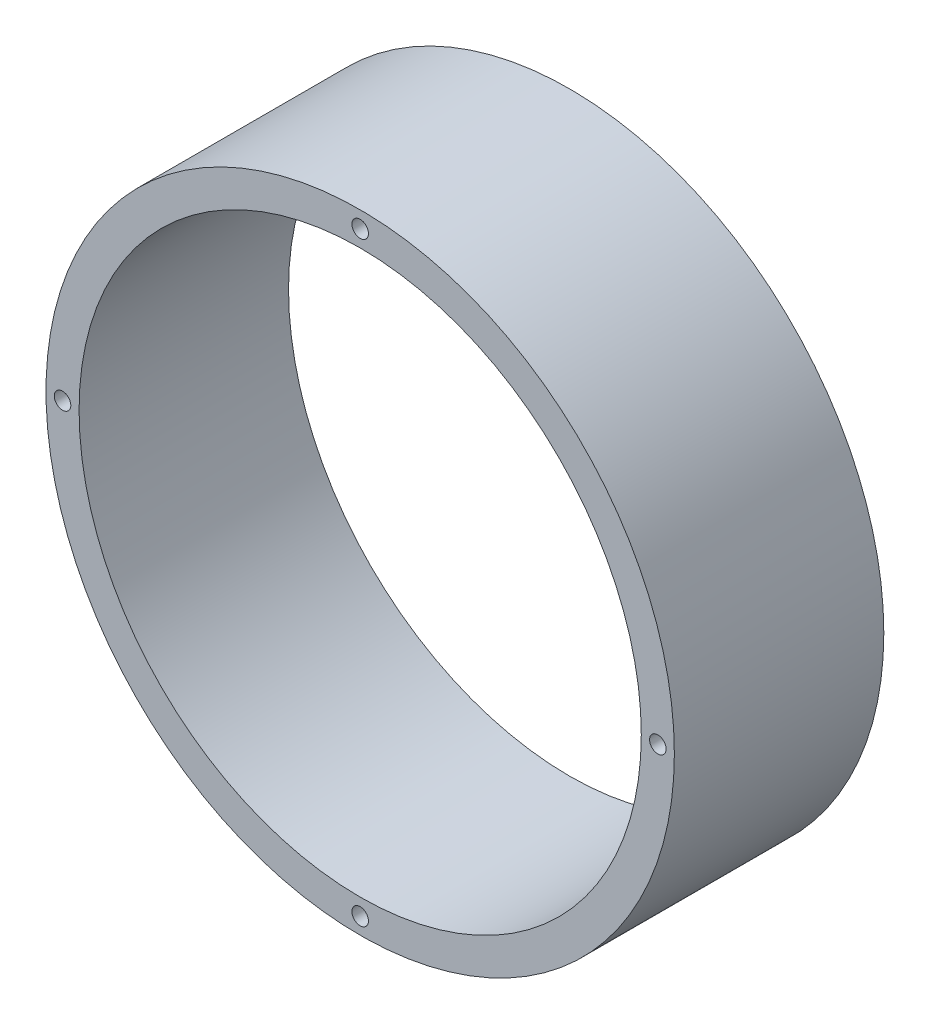
SolidWorks part; units mm, degrees
ref_plane "Front Plane" through (0, 0, 0) normal (0, 0, 1) x (1, 0, 0)
ref_plane "Top Plane" through (0, 0, 0) normal (0, 1, 0) x (1, 0, 0)
ref_plane "Right Plane" through (0, 0, 0) normal (1, 0, 0) x (0, 0, -1)
sketch "Sketch1" plane through (0, 0, 0) normal (0, 0, 1) x (1, 0, 0)
  circle A0 centre (0, 0) radius 57
  dimension "D1" = 114
extrude "Boss-Extrude1" add sketch "Sketch1" along normal blind 38
sketch "Sketch2" plane through (0, 0, 38) normal (0, 0, 1) x (1, 0, 0)
  circle A0 centre (0, 0) radius 51
  dimension "D1" = 102
extrude "Cut-Extrude1" cut sketch "Sketch2" against normal blind 39
sketch "Sketch4" plane through (0, 0, 0) normal (0, 0, -1) x (-1, 0, 0)
  circle A0 centre (0, 54) radius 1.5
  circle A1 centre (54, 0) radius 1.5
  circle A2 centre (0, -54) radius 1.5
  circle A3 centre (-54, 0) radius 1.5
  point P4 (0, 0)
  dimension "D2" = 3
  dimension "D1" = 54
  dimension "D3" = 4
extrude "Cut-Extrude3" cut sketch "Sketch4" against normal blind 15
ref_plane "Plane1" through (0, 0, 19) normal (0, 0, 1) x (1, 0, 0)
mirror "Mirror1" about plane through (0, 0, 19) normal (0, 0, 1) of "Cut-Extrude3"
